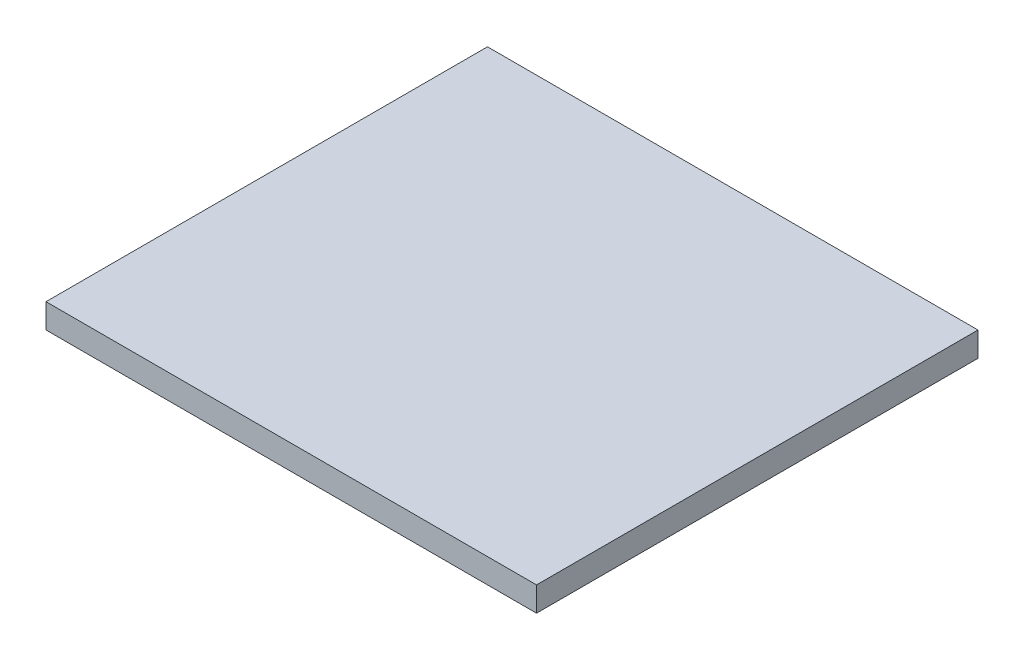
SolidWorks part; units mm, degrees
ref_plane "Front Plane" through (0, 0, 0) normal (0, 0, 1) x (1, 0, 0)
ref_plane "Top Plane" through (0, 0, 0) normal (0, 1, 0) x (1, 0, 0)
ref_plane "Right Plane" through (0, 0, 0) normal (1, 0, 0) x (0, 0, -1)
sketch "Sketch1" plane through (0, 0, 0) normal (0, 1, 0) x (1, 0, 0)
  line L0 (64.8373, 172.8232) -> (115.6373, 172.8232)
  line L9 (64.8373, 172.8232) -> (64.8373, 127.1032)
  line L10 (64.8373, 127.1032) -> (115.6373, 127.1032)
  line L11 (115.6373, 172.8232) -> (115.6373, 127.1032)
  dimension "D5" = 50.8
  dimension "D15" = 45.72
extrude "Boss-Extrude2" add sketch "Sketch1" along normal blind 2.54
